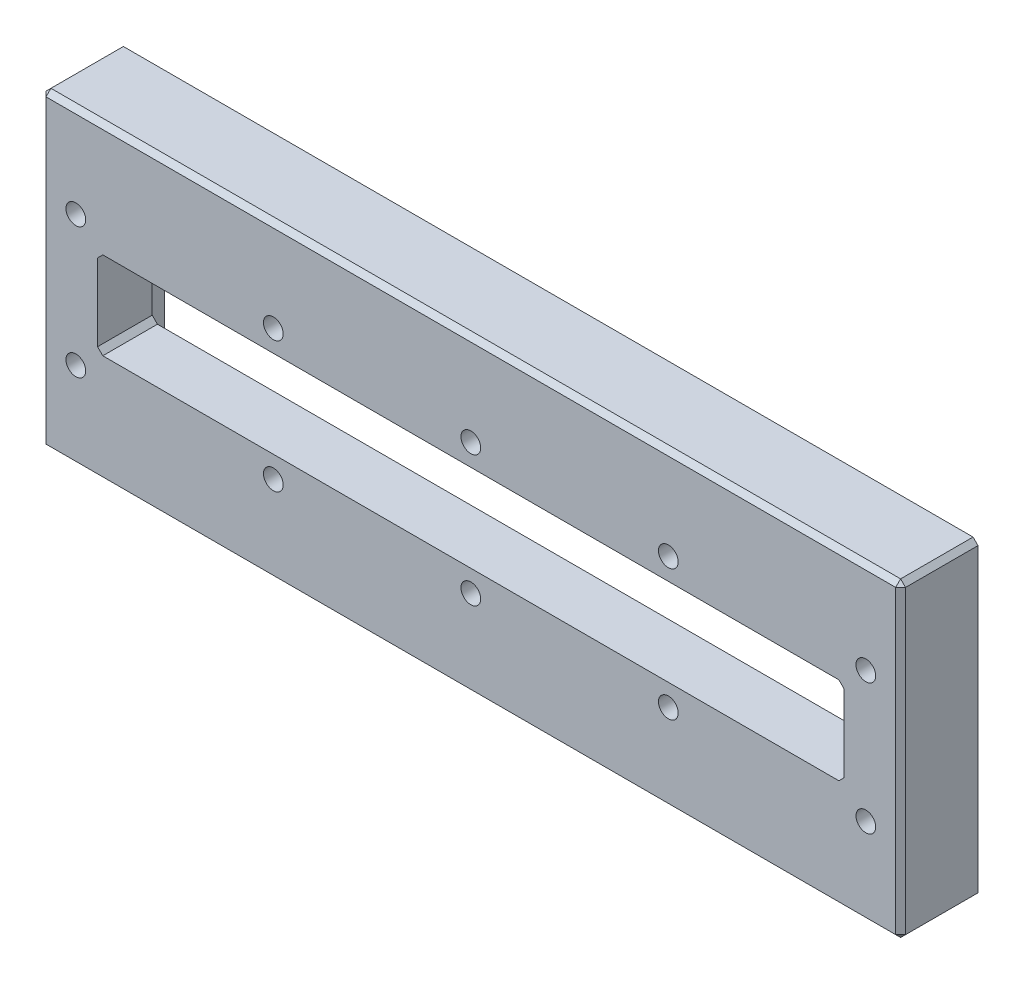
SolidWorks part; units mm, degrees
ref_plane "Front Plane" through (0, 0, 0) normal (0, 0, 1) x (1, 0, 0)
ref_plane "Top Plane" through (0, 0, 0) normal (0, 1, 0) x (1, 0, 0)
ref_plane "Right Plane" through (0, 0, 0) normal (1, 0, 0) x (0, 0, -1)
sketch "Sketch1" plane through (0, 0, 1006.65) normal (0, 0, 1) x (1, 0, 0)
  line L0 (-95.2094, -0.7315) -> (-95.2094, 52.1785) construction
  line L1 (-100.2094, 57.1785) -> (73.8806, 57.1785)
  line L2 (-100.2094, 57.1785) -> (-100.2094, -5.7315)
  line L3 (-100.2094, -5.7315) -> (73.8806, -5.7315)
  line L4 (73.8806, 57.1785) -> (73.8806, -5.7315)
  line L5 (-72.0644, 52.1785) -> (-44.2644, 52.1785) construction
  line L6 (68.8806, 52.1785) -> (68.8806, -0.7315) construction
  line L7 (45.7356, -0.7315) -> (17.9356, -0.7315) construction
  line L8 (-95.3094, 52.2785) -> (-95.3094, -0.8315)
  line L9 (-95.2094, 52.1785) -> (68.8806, 52.1785)
  line L10 (-95.2094, 52.1785) -> (-95.2094, -0.7315)
  line L11 (-95.2094, -0.7315) -> (68.8806, -0.7315)
  line L12 (68.8806, 52.1785) -> (68.8806, -0.7315)
  line L13 (-95.3094, -0.8315) -> (68.9806, -0.8315)
  line L14 (68.9806, 52.2785) -> (68.9806, -0.8315)
  line L15 (-95.3094, 52.2785) -> (68.9806, 52.2785)
  dimension "D1" = 5
  dimension "D2" = 5
  dimension "D3" = 5
  dimension "D4" = 5
  dimension "D5" = 0.1
extrude "Boss-Extrude1" add sketch "Sketch1" against normal up to surface (1.6 mm away) contours L4 L1 L2 L3 L8 L15 L14 L13
sketch "Sketch2" plane through (0, 0, 1006.65) normal (0, 0, 1) x (1, 0, 0)
  line L0 (-95.3094, 52.2785) -> (-95.3094, -0.8315) construction
  line L1 (-89.3094, 45.2785) -> (62.9806, 45.2785)
  line L2 (-89.3094, 45.2785) -> (-89.3094, 6.1685)
  line L3 (-89.3094, 6.1685) -> (62.9806, 6.1685)
  line L4 (62.9806, 45.2785) -> (62.9806, 6.1685)
  line L5 (-95.3094, -0.8315) -> (68.9806, -0.8315) construction
  line L6 (-95.3094, 52.2785) -> (68.9806, 52.2785) construction
  line L7 (68.9806, 52.2785) -> (68.9806, -0.8315) construction
  line L12 (73.8806, -5.7315) -> (73.8806, 57.1785)
  line L13 (73.8806, 57.1785) -> (-100.2094, 57.1785)
  line L14 (-100.2094, 57.1785) -> (-100.2094, -5.7315)
  line L15 (-100.2094, -5.7315) -> (73.8806, -5.7315)
  line L16 (73.8806, -5.7315) -> (73.8806, 57.1785)
  line L17 (73.8806, 57.1785) -> (-100.2094, 57.1785)
  line L18 (-100.2094, 57.1785) -> (-100.2094, -5.7315)
  line L19 (-100.2094, -5.7315) -> (73.8806, -5.7315)
  dimension "D1" = 6
  dimension "D2" = 7
  dimension "D3" = 7
  dimension "D4" = 6
  dimension "D5" = 0
extrude "Boss-Extrude2" add sketch "Sketch2" along normal blind 3
sketch "Sketch3" plane through (0, 0, 1009.65) normal (0, 0, 1) x (1, 0, 0)
  line L14 (-100.2094, -5.7315) -> (73.8806, -5.7315)
  line L15 (73.8806, -5.7315) -> (73.8806, 57.1785)
  line L16 (73.8806, 57.1785) -> (-100.2094, 57.1785)
  line L17 (-100.2094, 57.1785) -> (-100.2094, -5.7315)
  line L18 (-100.2094, -5.7315) -> (73.8806, -5.7315)
  line L19 (73.8806, -5.7315) -> (73.8806, 57.1785)
  line L20 (61.377, 34.2135) -> (-87.7058, 34.2135)
  line L21 (62.4356, 33.1549) -> (61.377, 34.2135)
  line L22 (62.4356, 24.6135) -> (62.4356, 33.1549)
  line L23 (62.4356, 17.5721) -> (62.4356, 24.6135)
  line L24 (61.377, 16.5135) -> (62.4356, 17.5721)
  line L25 (-87.7058, 16.5135) -> (61.377, 16.5135)
  line L26 (-88.7644, 17.5721) -> (-87.7058, 16.5135)
  line L27 (-88.7644, 24.6135) -> (-88.7644, 17.5721)
  line L28 (-87.7058, 34.2135) -> (-88.7644, 33.1549)
  line L29 (-88.7644, 33.1549) -> (-88.7644, 24.6135)
  line L30 (61.377, 34.2135) -> (-87.7058, 34.2135)
  line L31 (62.4356, 33.1549) -> (61.377, 34.2135)
  line L32 (62.4356, 24.6135) -> (62.4356, 33.1549)
  line L33 (62.4356, 17.5721) -> (62.4356, 24.6135)
  line L34 (61.377, 16.5135) -> (62.4356, 17.5721)
  line L35 (-87.7058, 16.5135) -> (61.377, 16.5135)
  line L36 (-88.7644, 17.5721) -> (-87.7058, 16.5135)
  line L37 (-88.7644, 24.6135) -> (-88.7644, 17.5721)
  line L38 (-87.7058, 34.2135) -> (-88.7644, 33.1549)
  line L39 (-88.7644, 33.1549) -> (-88.7644, 24.6135)
  line L40 (73.8806, 57.1785) -> (-100.2094, 57.1785)
  line L41 (-100.2094, 57.1785) -> (-100.2094, -5.7315)
  dimension "D1" = 0.1
  dimension "D2" = 0
extrude "Boss-Extrude3" add sketch "Sketch3" along normal up to surface (11.07 mm away)
sketch "Sketch4" plane through (0, 0, 1006.65) normal (0, 0, -1) x (-1, 0, 0)
  circle A0 centre (-46.8356, 50.6785) radius 0.8
  circle A1 centre (-16.8356, 50.6785) radius 0.8
  circle A2 centre (13.1644, 50.6785) radius 0.8
  circle A3 centre (43.1644, 50.6785) radius 0.8
  circle A4 centre (73.1644, 50.6785) radius 0.8
  circle A5 centre (73.1644, 0.7685) radius 0.8
  circle A6 centre (43.1644, 0.7685) radius 0.8
  circle A7 centre (13.1644, 0.7685) radius 0.8
  circle A8 centre (-16.8356, 0.7685) radius 0.8
  circle A9 centre (-46.8356, 0.7685) radius 0.8
  dimension "D1" = 1.6
extrude "Cut-Extrude1" cut sketch "Sketch4" against normal blind 10
sketch "Sketch5" plane through (0, 0, 1005.05) normal (0, 0, -1) x (-1, 0, 0)
  circle A0 centre (95.3094, 52.2785) radius 0.75
  circle A1 centre (95.3094, -0.8315) radius 0.75
  circle A2 centre (-68.9806, -0.8315) radius 0.75
  circle A3 centre (-68.9806, 52.2785) radius 0.75
  dimension "D1" = 1.5
extrude "Cut-Extrude2" cut sketch "Sketch5" against normal up to surface (1.6 mm away) up to face at (46.0356, 0.7685, 1006.65)
fillet "Fillet1" radius 1 8 edges at (68.2306, -0.8315, 1005.85) (68.9806, -0.0815, 1005.85) (-94.5594, -0.8315, 1005.85) (-95.3094, -0.0815, 1005.85) (-95.3094, 51.5285, 1005.85) (-94.5594, 52.2785, 1005.85) (68.9806, 51.5285, 1005.85) (68.2306, 52.2785, 1005.85)
sketch "Sketch6" plane through (0, 0, 1020.72) normal (0, 0, 1) x (1, 0, 0)
  circle A0 centre (-93.1644, 38.6135) radius 2
  circle A1 centre (-53.1644, 38.6135) radius 2
  circle A2 centre (-13.1644, 38.6135) radius 2
  circle A3 centre (26.8356, 38.6135) radius 2
  circle A4 centre (66.8356, 38.6135) radius 2
  circle A5 centre (66.8356, 12.1135) radius 2
  circle A6 centre (26.8356, 12.1135) radius 2
  circle A7 centre (-13.1644, 12.1135) radius 2
  circle A8 centre (-53.1644, 12.1135) radius 2
  circle A9 centre (-93.1644, 12.1135) radius 2
  dimension "D1" = 4
extrude "Cut-Extrude3" cut sketch "Sketch6" against normal blind 10
chamfer "Chamfer1" distance 1 angle 45 9 edges at (-100.2094, -5.7315, 1012.885) (-100.2094, 25.7235, 1005.05) (-100.2094, 25.7235, 1020.72) (-100.2094, 57.1785, 1012.885) (-13.1644, 57.1785, 1020.72) (73.8806, 57.1785, 1012.885) (73.8806, -5.7315, 1012.885) (73.8806, 25.7235, 1020.72) (-13.1644, -5.7315, 1020.72)
